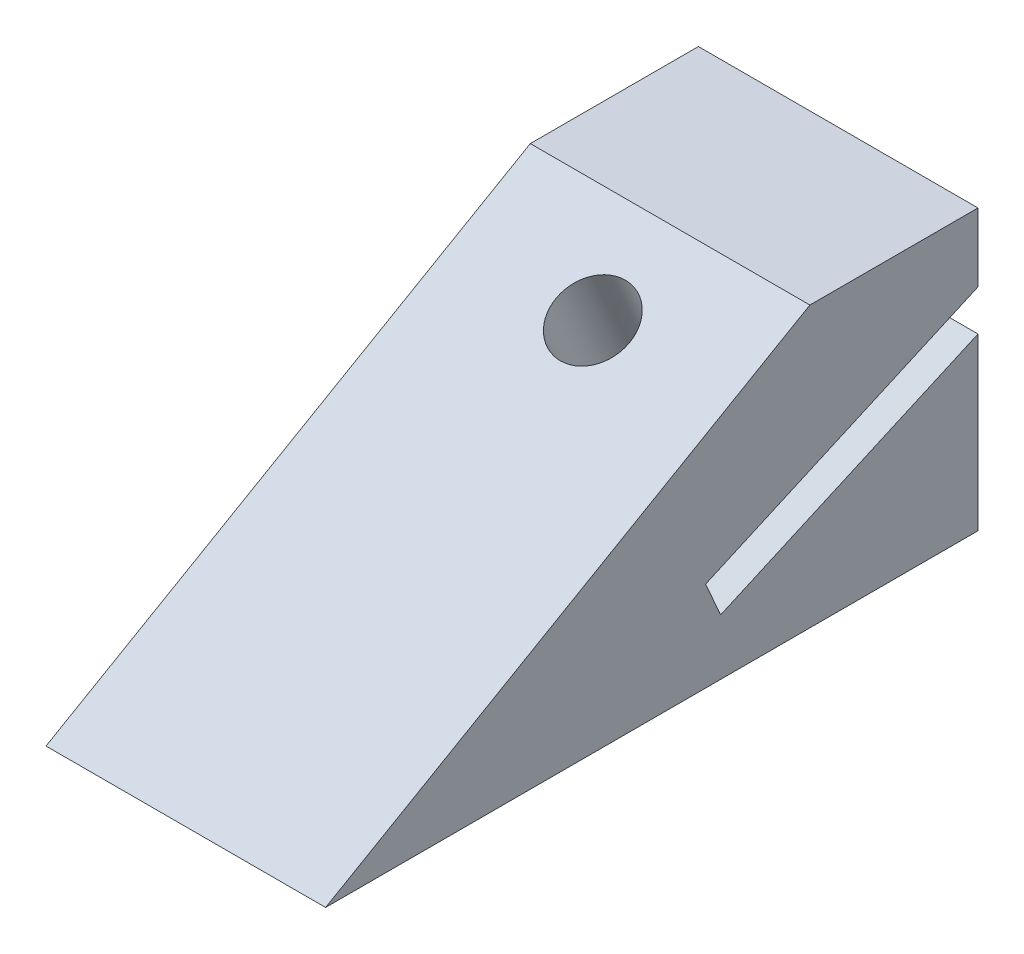
SolidWorks part; units mm, degrees
ref_plane "Front Plane" through (0, 0, 0) normal (0, 0, 1) x (1, 0, 0)
ref_plane "Top Plane" through (0, 0, 0) normal (0, 1, 0) x (1, 0, 0)
ref_plane "Right Plane" through (0, 0, 0) normal (1, 0, 0) x (0, 0, -1)
sketch "Sketch3" plane through (0, 0, 0) normal (1, 0, 0) x (0, 0, -1)
  line L0 (0, 0) -> (25.9808, 15)
  line L1 (35, 15) -> (35, 11.3349)
  line L2 (35, 0) -> (0, 0)
  line L3 (25.9808, 15) -> (35, 15)
  line L9 (20.3833, 4.8271) -> (35, 11.3349)
  line L11 (35, 9.1456) -> (21.1967, 3)
  line L12 (21.1967, 3) -> (20.3833, 4.8271)
  line L13 (35, 9.1456) -> (35, 0)
  dimension "D1" = 30
  dimension "D2" = 90
  dimension "D3" = 2
  dimension "D4" = 16
  dimension "D5" = 24
  dimension "D6" = 3
  dimension "D7" = 35
  dimension "D8" = 15
extrude "Boss-Extrude2" add sketch "Sketch3" along normal blind 15
sketch "Sketch7" plane through (0, -5.3724, -2.392) normal (0, 0.9135, 0.4067) x (1, 0, 0)
  line L0 (7.5, 38.0751) -> (7.5, 22.0751)
  line L1 (15, 38.0751) -> (0, 38.0751) construction
  circle A0 centre (7.5, 25.0751) radius 2
  dimension "D2" = 4
  dimension "D1" = 16
  dimension "D3" = 3
extrude "Cut-Extrude5" cut sketch "Sketch7" along normal blind 11 and the other way blind 2 contours L0 A0 | L0 A0
